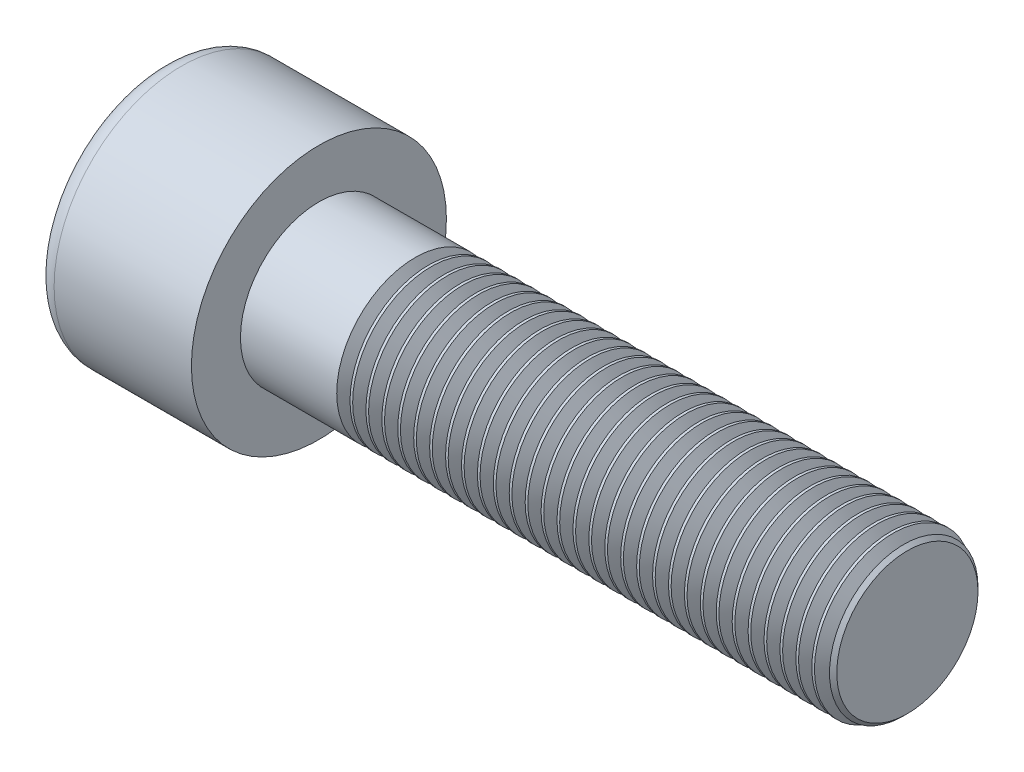
SolidWorks part; units mm, degrees
ref_plane "Front" through (0, 0, 0) normal (0, 0, 1) x (1, 0, 0)
ref_plane "Top" through (0, 0, 0) normal (0, 1, 0) x (1, 0, 0)
ref_plane "Right" through (0, 0, 0) normal (1, 0, 0) x (0, 0, -1)
sketch "Sketch1" plane through (0, 0, 0) normal (1, 0, 0) x (0, 0, -1)
  circle A0 centre (0, 0) radius 6.5
  dimension "dk" = 13
extrude "BaseHead" add sketch "Sketch1" along normal blind 8
sketch "Sketch2" plane through (8, 0, 0) normal (1, 0, 0) x (0, 0, -1)
  circle A0 centre (0, 0) radius 4
  dimension "d" = 8
extrude "BaseBody" add sketch "Sketch2" along normal blind 30
cosmetic thread "ThreadCosmetic1" [suppressed] parameters "b"=25, "D2"=6.647
sketch "Sketch3" plane through (0, 0, 0) normal (1, 0, 0) x (0, 0, -1)
  line L1 (3.4641, 0) -> (1.7321, 3)
  line L2 (1.7321, 3) -> (-1.7321, 3)
  line L3 (-1.7321, 3) -> (-3.4641, 0)
  line L4 (-3.4641, 0) -> (-1.7321, -3)
  line L5 (-1.7321, -3) -> (1.7321, -3)
  line L6 (1.7321, -3) -> (3.4641, 0)
  circle A0 centre (0, 0) radius 3 construction
  dimension "s" = 6
  dimension "e" = 6.9282
extrude "HexagonSocket" cut sketch "Sketch3" along normal blind 4
sketch "Sketch4" plane through (-4.1961, 0.75, 0) normal (0, 0, 1) x (-1, 0, 0)
  line L0 (-8.1961, 3.75) -> (-9.9282, 0.75)
  line L2 (-9.9282, 0.75) -> (-8.1961, 0.75)
  line L3 (-8.1961, 0.75) -> (-8.1961, 3.75)
  line L4 (-5.0351, 0.75) -> (0.839, 0.75) construction
  line L5 (-42.1961, 0.75) -> (-12.1961, 0.75) construction
  line L6 (-12.1961, 0.75) -> (-4.1961, 0.75) construction
  dimension "m" = 60
revolve "Cut-Revolve1" cut sketch "Sketch4" angle 360 about L4
fillet "HeadFillet" [suppressed] radius 0.4
fillet "TopFillet" radius 1 1 edges at (0, 0, -6.5)
chamfer "Chamfer1" distance 0.4 angle 45 1 edges at (38, 0, -4)
sketch "Sketch5" plane through (0, 0, 0) normal (0, 0, 1) x (1, 0, 0)
  line L0 (37.6, 3.4141) -> (37.9382, 4)
  line L1 (37.9382, 4) -> (37.9382, 4.6765)
  line L2 (37.9382, 4.6765) -> (37.2618, 4.6765)
  line L3 (37.2618, 4.6765) -> (37.2618, 4)
  line L4 (37.2618, 4) -> (37.6, 3.4141)
  line L5 (0, 0) -> (7.8886, 0) construction
  line L6 (37.6, -4) -> (37.6, 4) construction
  dimension "D1" = 8
  dimension "D2" = 0.6765
revolve "Cut-Revolve10" cut sketch "Sketch5" angle 360 about L5
pattern_linear "LPattern10" count 31 spacing 0.8118 along (-1, 0, 0) of "Cut-Revolve10"
equation "\"r1@TopFillet\" = \"d@Sketch2\" / 8"
equation "\"D1@Chamfer1\" = \"r@HeadFillet\""
equation "\"D1@Sketch5\" = \"d@Sketch2\""
equation "\"D2@Sketch5\" =  ( \"d@Sketch2\" - \"D2@ThreadCosmetic1\" )  / 2"
equation "\"D3@LPattern10\" = \"D2@Sketch5\" * 1.2"
equation "\"D1@LPattern10\" = \"b@ThreadCosmetic1\" / \"D3@LPattern10\""
